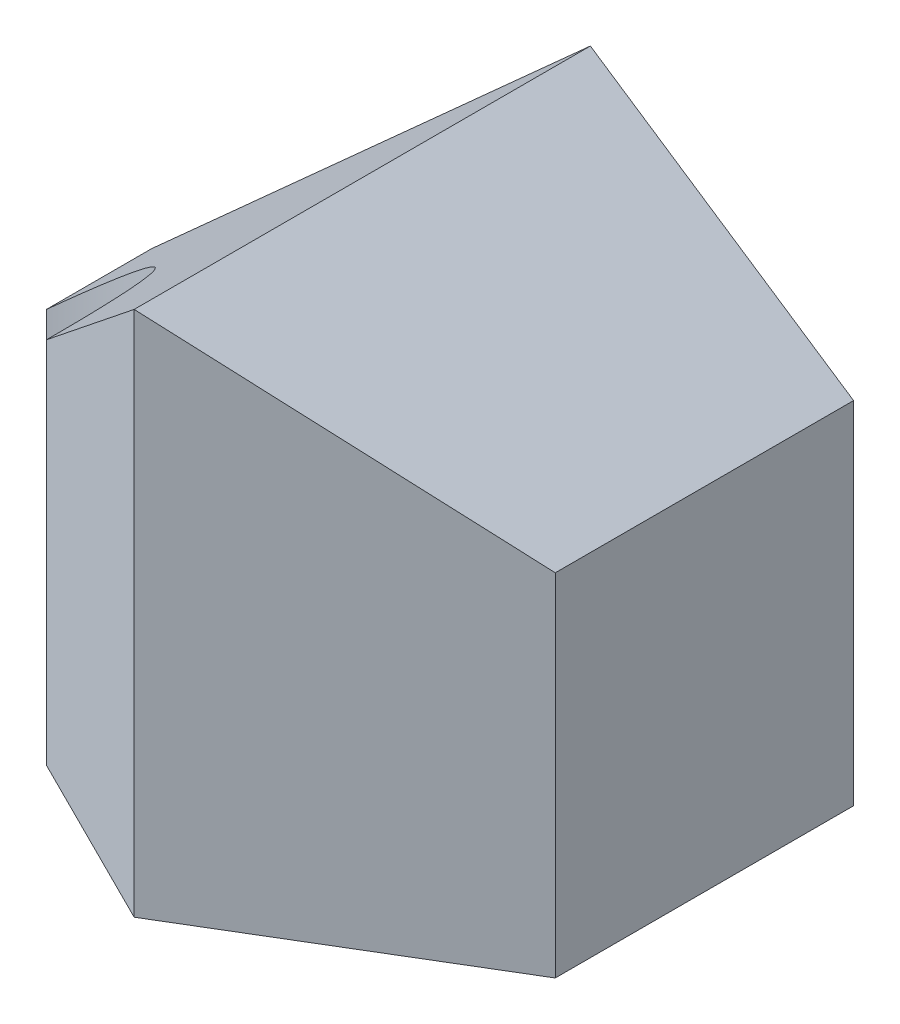
SolidWorks part; units mm, degrees
ref_plane "Front" through (0, 0, 0) normal (0, 0, 1) x (1, 0, 0)
ref_plane "Top" through (0, 0, 0) normal (0, 1, 0) x (1, 0, 0)
ref_plane "Right" through (0, 0, 0) normal (1, 0, 0) x (0, 0, -1)
sketch "Sketch1" plane through (0, 0, 0) normal (0, 1, 0) x (1, 0, 0)
  line L2 (0, 40) -> (0, 52)
  line L3 (0, 52) -> (80, 52)
  line L5 (80, 18) -> (80, 52)
  line L7 (80, 18) -> (50, 0)
  line L8 (30, 10) -> (50, 0)
  arc A0 (30, 10) -> (0, 40) centre (0, 10) ccw
extrude "Extrude1" add sketch "Sketch1" along normal blind 60
sketch "Sketch2" plane through (0, 0, 0) normal (0, 0, 1) x (1, 0, 0)
  line L1 (80, 60) -> (80, 0) construction
  line L2 (50, 60) -> (80, 40)
  line L3 (80, 40) -> (80, 60)
  line L4 (80, 60) -> (50, 60)
  line L5 (50, 60) -> (0, 60)
  line L6 (0, 60) -> (0, 15)
  line L7 (0, 60) -> (0, 0) construction
  line L8 (0, 15) -> (50, 60)
  dimension "D1" = 20
  dimension "D2" = 45
extrude "Cut-Extrude1" cut sketch "Sketch2" against normal through all contours L6 L8 L5 | L3 L4 L2
